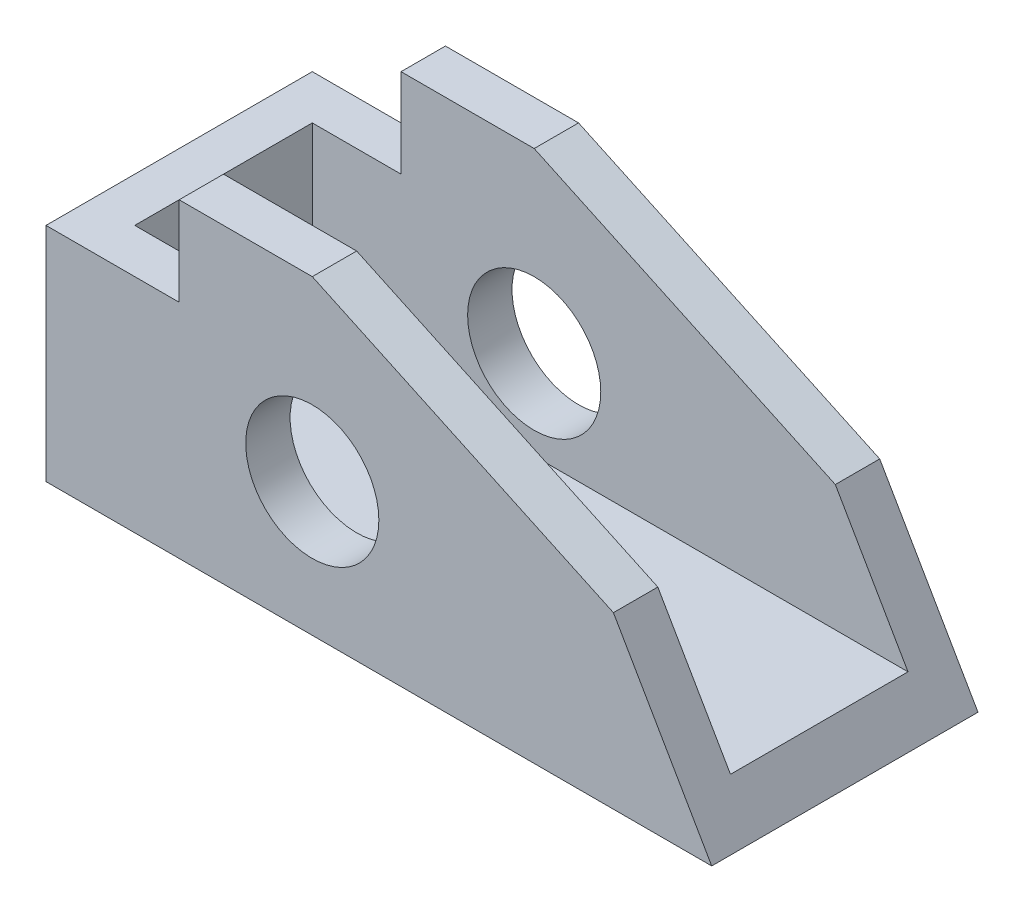
SolidWorks part; units mm, degrees
ref_plane "Front Plane" through (0, 0, 0) normal (0, 0, 1) x (1, 0, 0)
ref_plane "Top Plane" through (0, 0, 0) normal (0, 1, 0) x (1, 0, 0)
ref_plane "Right Plane" through (0, 0, 0) normal (1, 0, 0) x (0, 0, -1)
sketch "Sketch1" plane through (0, 0, 0) normal (0, 0, 1) x (1, 0, 0)
  line L0 (0, 0) -> (95.25, 0)
  line L1 (95.25, 0) -> (81.1867, 24.3583)
  line L2 (81.1867, 24.3583) -> (38.1, 44.45)
  line L3 (38.1, 44.45) -> (19.05, 44.45)
  line L4 (19.05, 44.45) -> (19.05, 31.75)
  line L5 (19.05, 31.75) -> (0, 31.75)
  line L6 (0, 31.75) -> (0, 0)
  dimension "D1" = 31.75
  dimension "D2" = 44.45
  dimension "D3" = 19.05
  dimension "D4" = 38.1
  dimension "D5" = 95.25
  dimension "D6" = 60
  dimension "D7" = 25
extrude "Boss-Extrude1" add sketch "Sketch1" against normal blind 38.1
sketch "Sketch2" plane through (0, 0, 0) normal (0, 0, 1) x (1, 0, 0)
  line L0 (0, 0) -> (95.25, 0) construction
  line L1 (0, 31.75) -> (0, 0) construction
  circle A0 centre (38.1, 19.05) radius 9.525
  dimension "D1" = 19.05
  dimension "D2" = 19.05
  dimension "D3" = 38.1
extrude "Cut-Extrude1" cut sketch "Sketch2" against normal through all
sketch "Sketch3" plane through (0, 44.45, 0) normal (0, 1, 0) x (1, 0, 0)
  line L0 (0, 38.1) -> (0, 0) construction
  line L1 (6.35, 31.75) -> (95.25, 31.75)
  line L2 (6.35, 31.75) -> (6.35, 6.35)
  line L3 (6.35, 6.35) -> (95.25, 6.35)
  line L4 (95.25, 31.75) -> (95.25, 6.35)
  line L5 (95.25, 38.1) -> (95.25, 0) construction
  line L6 (81.1867, 38.1) -> (38.1, 38.1) construction
  line L7 (81.1867, 0) -> (38.1, 0) construction
  dimension "D1" = 6.35
  dimension "D2" = 0
  dimension "D3" = 6.35
  dimension "D4" = 6.35
extrude "Cut-Extrude2" cut sketch "Sketch3" against normal blind 38.1
equation "\"60degdeg\"=47.4761"
